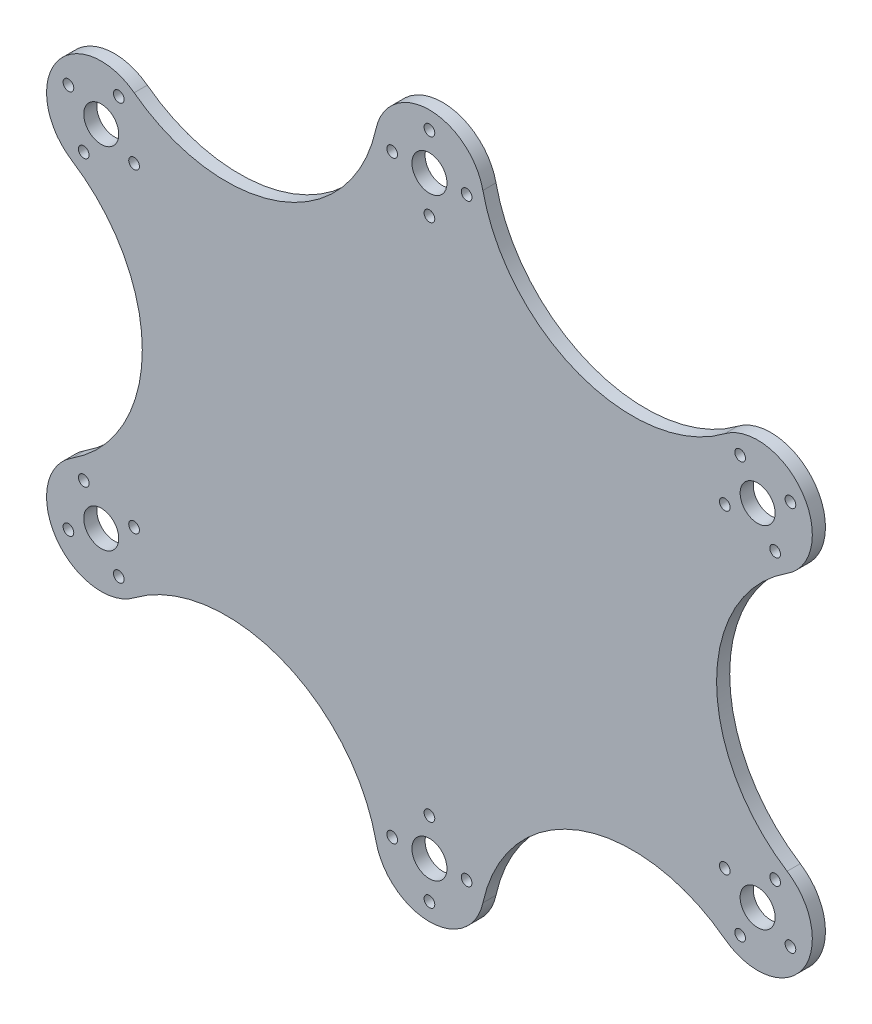
SolidWorks part; units mm, degrees
material "1345 Alloy"
ref_plane "Front Plane" through (0, 0, 0) normal (0, 0, 1) x (1, 0, 0)
ref_plane "Top Plane" through (0, 0, 0) normal (0, 1, 0) x (1, 0, 0)
ref_plane "Right Plane" through (0, 0, 0) normal (1, 0, 0) x (0, 0, -1)
sketch "Sketch2" plane through (0, 0, 0) normal (0, 0, 1) x (1, 0, 0)
  circle A0 centre (-44.7867, 41.5877) radius 4
  circle A1 centre (30.2133, 69.4265) radius 4
  circle A2 centre (105.2133, 41.5877) radius 4
  circle A3 centre (105.2133, -38.4123) radius 4
  circle A4 centre (30.2133, -66.2511) radius 4
  circle A5 centre (-44.7867, -38.4123) radius 4
  arc A6 (-37.2642, 51.5708) -> (-51.5281, 31.0614) centre (-44.7867, 41.5877) ccw
  arc A7 (42.4276, 72.0836) -> (17.9989, 72.0836) centre (30.2133, 69.4265) ccw
  arc A8 (-51.5281, -27.886) -> (-37.2642, -48.3954) centre (-44.7867, -38.4123) ccw
  arc A9 (17.9989, -68.9082) -> (42.4276, -68.9082) centre (30.2133, -66.2511) ccw
  arc A10 (97.6908, -48.3954) -> (111.9547, -27.886) centre (105.2133, -38.4123) ccw
  arc A11 (111.9547, 31.0614) -> (97.6908, 51.5708) centre (105.2133, 41.5877) ccw
  arc A12 (-51.5281, -27.886) -> (-51.5281, 31.0614) centre (-70.4041, 1.5877) ccw
  arc A14 (-37.2642, 51.5708) -> (17.9989, 72.0836) centre (-16.2012, 79.5234) ccw
  arc A15 (42.4276, 72.0836) -> (97.6908, 51.5708) centre (76.6277, 79.5234) ccw
  arc A16 (111.9547, 31.0614) -> (111.9547, -27.886) centre (130.8306, 1.5877) ccw
  arc A17 (97.6908, -48.3954) -> (42.4276, -68.9082) centre (76.6277, -76.348) ccw
  arc A19 (17.9989, -68.9082) -> (-37.2642, -48.3954) centre (-16.2012, -76.348) ccw
  circle A20 centre (30.2133, 77.9265) radius 1.22
  circle A21 centre (21.7133, 69.4265) radius 1.22
  circle A22 centre (30.2133, 60.9265) radius 1.22
  circle A23 centre (38.7133, 69.4265) radius 1.22
  circle A28 centre (-40.7867, 49.0877) radius 1.22
  circle A29 centre (-37.2867, 37.5877) radius 1.22
  circle A30 centre (-48.7867, 34.0877) radius 1.22
  circle A31 centre (-52.2867, 45.5877) radius 1.22
  circle A32 centre (-37.2867, -34.4123) radius 1.22
  circle A33 centre (-48.7867, -30.9123) radius 1.22
  circle A34 centre (-40.7867, -45.9123) radius 1.22
  circle A35 centre (-52.2867, -42.4123) radius 1.22
  circle A36 centre (112.7133, -42.4123) radius 1.22
  circle A37 centre (101.2133, -45.9123) radius 1.22
  circle A38 centre (97.7133, -34.4123) radius 1.22
  circle A39 centre (109.2133, -30.9123) radius 1.22
  circle A40 centre (97.7133, 37.5877) radius 1.22
  circle A41 centre (109.2133, 34.0877) radius 1.22
  circle A42 centre (101.2133, 49.0877) radius 1.22
  circle A43 centre (112.7133, 45.5877) radius 1.22
  circle A44 centre (30.2133, -57.7511) radius 1.22
  circle A45 centre (38.7133, -66.2511) radius 1.22
  circle A46 centre (21.7133, -66.2511) radius 1.22
  circle A47 centre (30.2133, -74.7511) radius 1.22
  point P17 (-55.0489, 48.7248)
  point P38 (-55.0489, -45.5495)
  point P43 (115.4754, 48.7248)
  dimension "D7" = 8
  dimension "D8" = 8
  dimension "D9" = 8
  dimension "D10" = 8
  dimension "D11" = 8
  dimension "D12" = 8
  dimension "D13" = 25
  dimension "D14" = 2.44
  dimension "D15" = 25
  dimension "D16" = 25
  dimension "D17" = 25
  dimension "D18" = 25
  dimension "D19" = 2.44
  dimension "D20" = 2.44
  dimension "D21" = 8.5
  dimension "D22" = 8.5
  dimension "D23" = 2.44
  dimension "D24" = 8.5
  dimension "D25" = 8.5
  dimension "D1" = 150
  dimension "D2" = 80
  dimension "D3" = 80
  dimension "D4" = 80
  dimension "D5" = 80
  dimension "D6" = 80
extrude "Boss-Extrude2" add sketch "Sketch2" along normal blind 3
